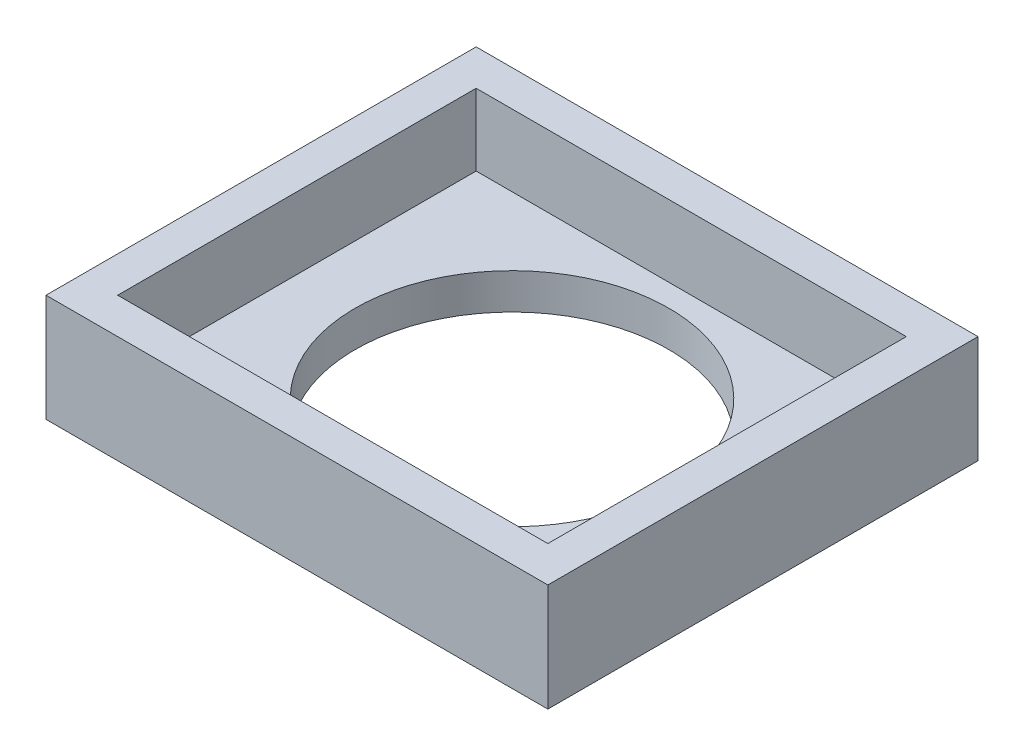
SolidWorks part; units mm, degrees
ref_plane "Front Plane" through (0, 0, 0) normal (0, 0, 1) x (1, 0, 0)
ref_plane "Top Plane" through (0, 0, 0) normal (0, 1, 0) x (1, 0, 0)
ref_plane "Right Plane" through (0, 0, 0) normal (1, 0, 0) x (0, 0, -1)
sketch "Sketch1" plane through (0, 0, 0) normal (0, 1, 0) x (1, 0, 0)
  line L1 (-12, 10) -> (12, 10) construction
  line L2 (-12, 10) -> (-12, -10) construction
  line L3 (-12, -10) -> (12, -10) construction
  line L4 (12, 10) -> (12, -10) construction
  line L5 (-12, 10) -> (12, -10) construction
  line L6 (-12, -10) -> (12, 10) construction
  line L7 (-14, 12) -> (14, 12)
  line L8 (-14, 12) -> (-14, -12)
  line L9 (-14, -12) -> (14, -12)
  line L10 (14, 12) -> (14, -12)
  line L11 (-14, 12) -> (14, -12) construction
  line L12 (-14, -12) -> (14, 12) construction
  circle A0 centre (0, 0) radius 8.75
  point P0 (0, 0)
  dimension "D1" = 17.5
  dimension "D2" = 24
  dimension "D3" = 20
  dimension "D4" = 2
  dimension "D5" = 2
extrude "Boss-Extrude1" add sketch "Sketch1" along normal blind 2
sketch "Sketch2" plane through (0, 2, 0) normal (0, 1, 0) x (1, 0, 0)
  line L0 (12, -10) -> (12, 10)
  line L1 (12, 10) -> (-12, 10)
  line L2 (-12, 10) -> (-12, -10)
  line L3 (-12, -10) -> (12, -10)
  line L4 (14, -12) -> (14, 12)
  line L5 (14, 12) -> (-14, 12)
  line L6 (-14, 12) -> (-14, -12)
  line L7 (-14, -12) -> (14, -12)
  line L8 (14, -12) -> (14, 12)
  line L9 (14, 12) -> (-14, 12)
  line L10 (-14, 12) -> (-14, -12)
  line L11 (-14, -12) -> (14, -12)
  dimension "D1" = 0
  dimension "D2" = 2
extrude "Boss-Extrude2" add sketch "Sketch2" along normal blind 4
